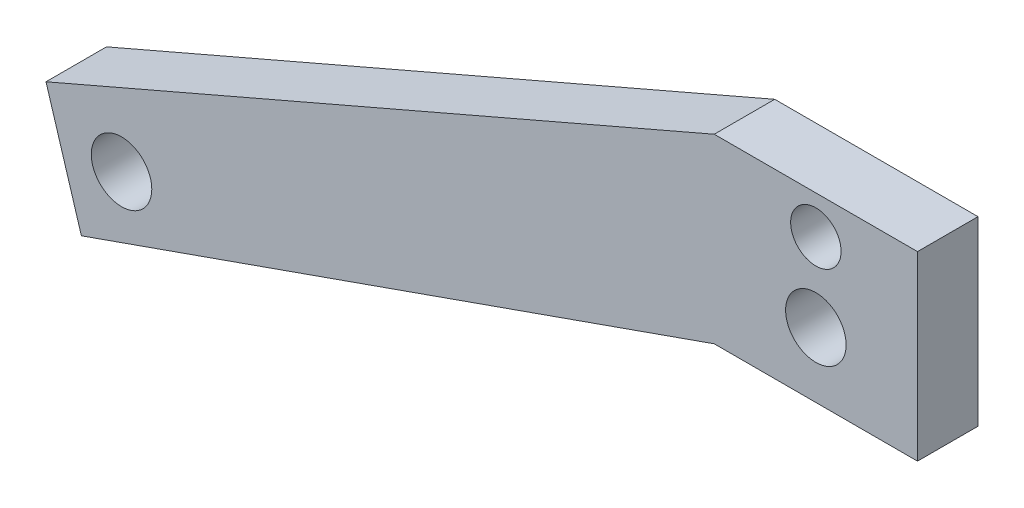
SolidWorks part; units mm, degrees
ref_plane "Front Plane" through (0, 0, 0) normal (0, 0, 1) x (1, 0, 0)
ref_plane "Top Plane" through (0, 0, 0) normal (0, 1, 0) x (1, 0, 0)
ref_plane "Right Plane" through (0, 0, 0) normal (1, 0, 0) x (0, 0, -1)
sketch "Sketch1" plane through (0, 0, 0) normal (0, 0, 1) x (1, 0, 0)
  line L0 (-16, 45) -> (-121.1993, -0.4465)
  line L2 (-276.7879, -13.7826) -> (-251.7788, -35.3348) construction
  line L3 (0, 26.6476) -> (-109.3056, -6.7705) construction
  line L4 (-16, 45) -> (-16, 15)
  line L5 (-16, 15) -> (16, 15)
  line L6 (16, 15) -> (16, 45)
  line L7 (16, 45) -> (-16, 45)
  line L8 (-16, 45) -> (-16, 16.425) construction
  line L9 (-16, 15) -> (16, 15) construction
  line L10 (16, 16.425) -> (16, 45)
  line L11 (16, 45) -> (-16, 45)
  line L12 (16, 16.425) -> (-16, 16.425)
  line L13 (-16, 16.425) -> (-115.6296, -18.6642)
  line L14 (-115.6296, -18.6642) -> (-121.1993, -0.4465)
  line L15 (-251.7788, -35.3348) -> (-242.2031, -37.4927) construction
  line L17 (-28.3991, 26.6361) -> (-28.037, 26.7) construction
  line L18 (-2117.156, -341.6) -> (-28.037, 26.7) construction
  line L19 (-242.2031, -37.4927) -> (-208.8903, -37.4927) construction
  line L20 (-208.8903, -37.4927) -> (-16, 45) construction
  line L21 (-292.5067, -43.5335) -> (-248.9466, -55.1606) construction
  line L22 (-248.9466, -55.1606) -> (-208.8903, -56.2396) construction
  line L23 (-208.8903, -56.2396) -> (-14.9476, 16.425) construction
  line L24 (-288.0555, -26.8574) -> (0, 26.6476) construction
  line L47 (-109.3056, -6.7705) -> (-118.4144, -9.5554) construction
  circle A0 centre (0, 39) radius 3.9688 construction
  circle A1 centre (0, 39) radius 3.9688
  circle A2 centre (0, 26.6476) radius 4.7625
  circle A3 centre (-109.3056, -6.7705) radius 4.7625
  circle A4 centre (-288.0555, -26.8574) radius 17.26 construction
  point P19 (0, 0)
  point P21 (-118.4144, -9.5554)
  point P22 (-37.2984, 17.3696)
  dimension "D2" = 9.525
  dimension "D4" = 114.3
  dimension "D7" = 292.9825
  dimension "D3" = 9.525
  dimension "D5" = 19.05
  dimension "D6" = 28.575
  dimension "D8" = 17
  dimension "D9" = 32
  dimension "D1" = 0
extrude "Boss-Extrude1" add sketch "Sketch1" along normal blind 9.525
